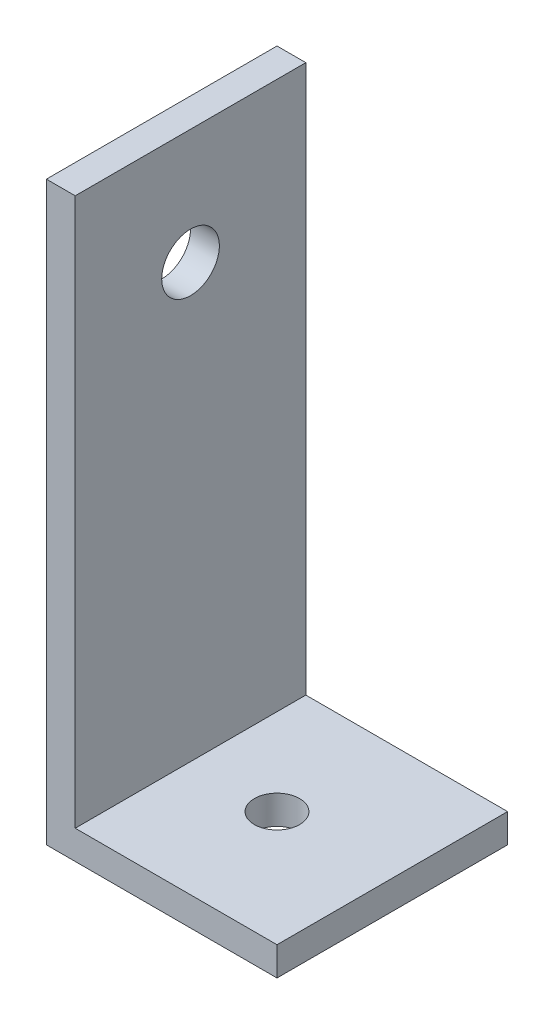
SolidWorks part; units mm, degrees
material "6061-T6 (SS)"
ref_plane "Front Plane" through (0, 0, 0) normal (0, 0, 1) x (1, 0, 0)
ref_plane "Top Plane" through (0, 0, 0) normal (0, 1, 0) x (1, 0, 0)
ref_plane "Right Plane" through (0, 0, 0) normal (1, 0, 0) x (0, 0, -1)
sketch "Sketch1" plane through (0, 0, 0) normal (0, 0, 1) x (1, 0, 0)
  line L0 (0, 0) -> (0, 63.5)
  line L1 (0, 63.5) -> (3.175, 63.5)
  line L2 (3.175, 63.5) -> (3.175, 3.175)
  line L3 (3.175, 3.175) -> (25.4, 3.175)
  line L4 (25.4, 3.175) -> (25.4, 0)
  line L5 (25.4, 0) -> (0, 0)
  dimension "D1" = 63.5
  dimension "D2" = 25.4
  dimension "D3" = 3.175
extrude "Boss-Extrude1" add sketch "Sketch1" along normal blind 25.4
sketch "Sketch2" plane through (0, 0, 0) normal (-1, 0, 0) x (0, 0, 1)
  line L0 (25.4, 0) -> (0, 0) construction
  line L1 (0, 63.5) -> (0, 0) construction
  circle A0 centre (12.7, 50.8) radius 3.175
  dimension "D1" = 50.8
  dimension "D2" = 12.7
  dimension "D3" = 6.35
extrude "Cut-Extrude1" cut sketch "Sketch2" against normal through all
hole_wizard "#9 (0.196) Diameter Hole1" positions "Sketch3" profile "Sketch4" hole size "#9" standard "ANSI Inch" end condition up to next
sketch "Sketch3" plane through (0, 0, 0) normal (0, -1, 0) x (-1, 0, 0)
  line L0 (0, -25.4) -> (-25.4, -25.4) construction
  line L1 (0, -25.4) -> (0, 0) construction
  point P0 (-12.7, -12.7)
  dimension "D1" = 12.7
  dimension "D2" = 12.7
sketch "Sketch4" plane through (12.7, 0, 12.7) normal (1, 0, 0) x (0, 0, -1)
  line L0 (0, 0) -> (0, 3.175)
  line L1 (0, 3.175) -> (2.4892, 3.175)
  line L2 (2.4892, 3.175) -> (2.4892, 0)
  line L5 (2.4892, 0) -> (0, 0)
  line L11 (0, -6.35) -> (0, 107.95) construction
  dimension "Thru Hole Dia." = 4.9784
  dimension "Thru Hole Depth" = 3.175
equation "\"Thick\"= \"in\""
